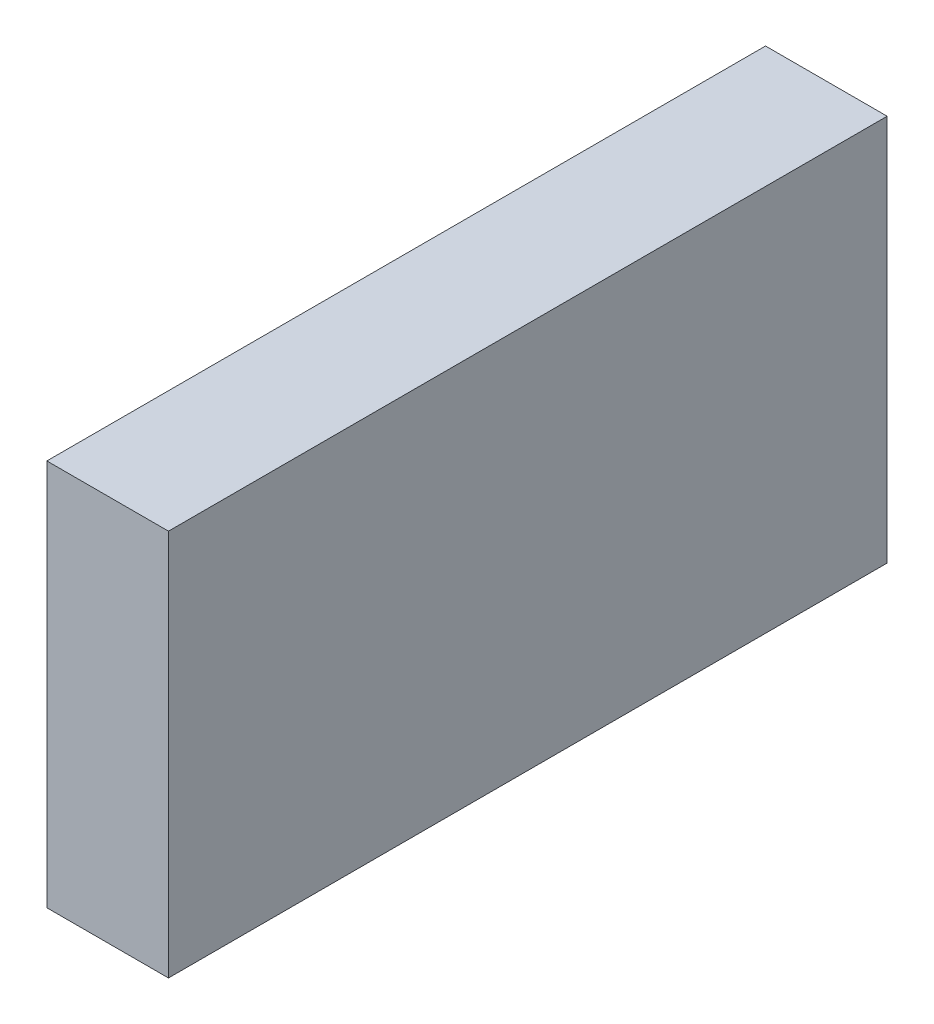
SolidWorks part; units mm, degrees
ref_plane "Face" through (0, 0, 0) normal (0, 0, 1) x (1, 0, 0)
ref_plane "Dessus" through (0, 0, 0) normal (0, 1, 0) x (1, 0, 0)
ref_plane "Droite" through (0, 0, 0) normal (1, 0, 0) x (0, 0, -1)
sketch "Esquisse1" plane through (0, 0, 0) normal (0, 1, 0) x (1, 0, 0)
  line L1 (0, 0) -> (22, 0)
  line L2 (0, 0) -> (0, 130)
  line L3 (0, 130) -> (22, 130)
  line L4 (22, 0) -> (22, 130)
  dimension "D1" = 130
  dimension "D2" = 22
extrude "Extrusion1" add sketch "Esquisse1" along normal blind 70
